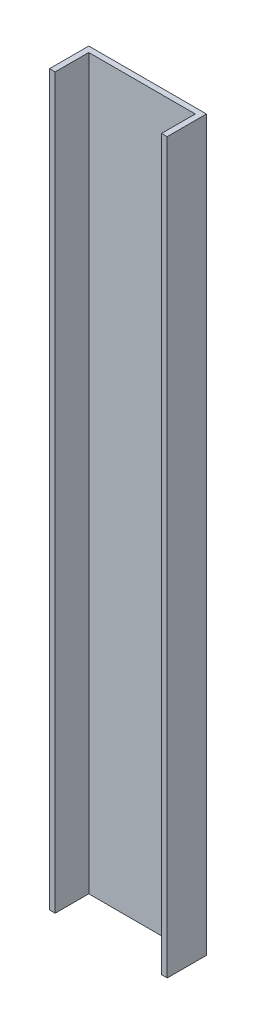
SolidWorks part; units mm, degrees
ref_plane "Front Plane" through (0, 0, 0) normal (0, 0, 1) x (1, 0, 0)
ref_plane "Top Plane" through (0, 0, 0) normal (0, 1, 0) x (1, 0, 0)
ref_plane "Right Plane" through (0, 0, 0) normal (1, 0, 0) x (0, 0, -1)
ref_plane "Plane1" through (0, 2350, 0) normal (0, 1, 0) x (1, 0, 0)
sketch "Sketch1" plane through (0, 2350, 0) normal (0, 1, 0) x (1, 0, 0)
  line L0 (-10, 70) -> (-10, 0)
  line L1 (-10, 0) -> (0, 0)
  line L2 (0, 0) -> (0, 60)
  line L3 (0, 60) -> (190, 60)
  line L4 (190, 60) -> (190, 0)
  line L5 (190, 0) -> (200, 0)
  line L6 (200, 0) -> (200, 70)
  line L7 (200, 70) -> (-10, 70)
extrude "Boss-Extrude1" add sketch "Sketch1" against normal blind 1300
